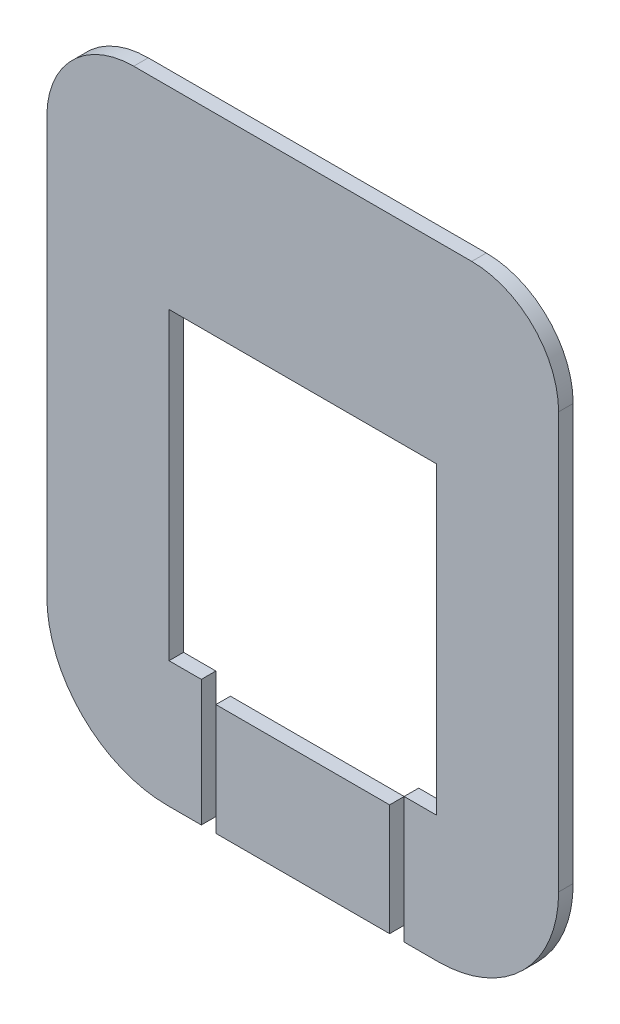
SolidWorks part; units mm, degrees
ref_plane "Front Plane" through (0, 0, 0) normal (0, 0, 1) x (1, 0, 0)
ref_plane "Top Plane" through (0, 0, 0) normal (0, 1, 0) x (1, 0, 0)
ref_plane "Right Plane" through (0, 0, 0) normal (1, 0, 0) x (0, 0, -1)
sketch "Sketch1" plane through (0, 0, 0) normal (0, 0, 1) x (1, 0, 0)
  line L0 (0, 96.5) -> (0, -96.5) construction
  line L1 (-80, 96.5) -> (80, 96.5) construction
  line L2 (-80, 96.5) -> (-80, -96.5) construction
  line L3 (-80, -96.5) -> (80, -96.5) construction
  line L4 (80, 96.5) -> (80, -96.5) construction
  line L5 (-50, 96.5) -> (50, 96.5) construction
  line L6 (-40, -96.5) -> (40, -96.5) construction
  line L7 (-80, 66.5) -> (80, 66.5) construction
  line L8 (-80, 66.5) -> (-80, -56.5) construction
  line L9 (-80, -56.5) -> (80, -56.5) construction
  line L10 (80, 66.5) -> (80, -56.5) construction
  line L11 (-0.5, -96.5) -> (0.5, -96.5) construction
  line L12 (-40, -96.5) -> (-0.5, -96.5) construction
  line L13 (0.5, -96.5) -> (40, -96.5) construction
  line L14 (0.5, -92.2) -> (40, -92.2)
  line L15 (75.7, 66.5) -> (75.7, -56.5)
  line L16 (-50, 92.2) -> (50, 92.2)
  line L17 (-75.7, 66.5) -> (-75.7, -56.5)
  line L18 (-40, -92.2) -> (-0.5, -92.2)
  line L19 (-0.5, -92.2) -> (0.5, -92.2)
  arc A0 (-80, 66.5) -> (-50, 96.5) centre (-50, 66.5) cw construction
  arc A1 (50, 96.5) -> (80, 66.5) centre (50, 66.5) cw construction
  arc A2 (-80, -56.5) -> (-40, -96.5) centre (-40, -56.5) ccw construction
  arc A3 (40, -96.5) -> (80, -56.5) centre (40, -56.5) ccw construction
  arc A4 (40, -92.2) -> (75.7, -56.5) centre (40, -56.5) ccw
  arc A5 (50, 92.2) -> (75.7, 66.5) centre (50, 66.5) cw
  arc A6 (-75.7, 66.5) -> (-50, 92.2) centre (-50, 66.5) cw
  arc A7 (-75.7, -56.5) -> (-40, -92.2) centre (-40, -56.5) ccw
  point P6 (0, 0)
  point P10 (0, 96.5)
  point P19 (0, -96.5)
  point P23 (0, -96.5)
  dimension "D3" = 40
  dimension "D4" = 30
  dimension "D1" = 193
  dimension "D2" = 160
  dimension "D5" = 1
  dimension "D6" = 4.3
extrude "Boss-Extrude1" add sketch "Sketch1" along normal blind 4.3
sketch "Sketch2" plane through (0, 0, 4.3) normal (0, 0, 1) x (1, 0, 0)
  line L0 (-40, -92.2) -> (40, -92.2) construction
  line L1 (-39.555, 35.11) -> (39.555, 35.11)
  line L2 (-39.555, 35.11) -> (-39.555, -54.89)
  line L3 (-39.555, -54.89) -> (39.555, -54.89)
  line L4 (39.555, 35.11) -> (39.555, -54.89)
  line L6 (-30, -54.89) -> (30, -54.89)
  line L7 (-30, -54.89) -> (-30, -59.19)
  line L8 (-30, -59.19) -> (30, -59.19)
  line L9 (30, -54.89) -> (30, -59.19)
  line L10 (-30, -59.19) -> (-25.7, -59.19)
  line L11 (-30, -59.19) -> (-30, -92.2)
  line L12 (-30, -92.2) -> (-25.7, -92.2)
  line L13 (-25.7, -59.19) -> (-25.7, -92.2)
  line L14 (30, -59.19) -> (25.7, -59.19)
  line L15 (30, -59.19) -> (30, -92.2)
  line L16 (30, -92.2) -> (25.7, -92.2)
  line L17 (25.7, -59.19) -> (25.7, -92.2)
  point P4 (0, -54.89)
  point P18 (0, -59.19)
  line M5 (-40, -92.2) -> (40, -92.2)
  dimension "D1" = 90
  dimension "D2" = 79.11
  dimension "D3" = 37.31
  dimension "D4" = 4.3
  dimension "D5" = 4.3
  dimension "D6" = 60
  dimension "D7" = 4.3
extrude "Cut-Extrude1" cut sketch "Sketch2" against normal blind 10 contours L4 L1 L2 L3 | L9 L3 L7 L8 | L13 L8 L11 M5 | L8 L17 L15 M5
